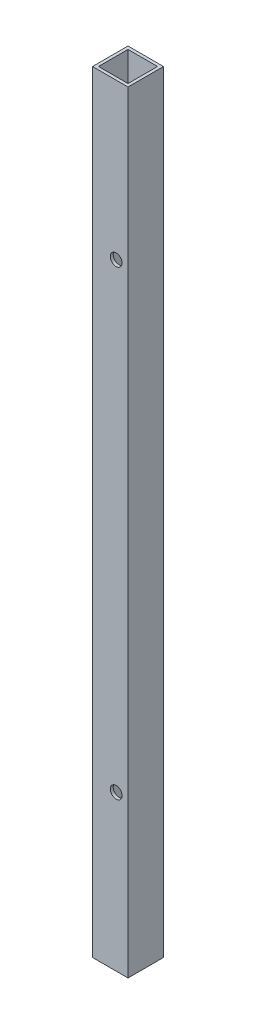
SolidWorks part; units mm, degrees
ref_plane "Front" through (0, 0, 0) normal (0, 0, 1) x (1, 0, 0)
ref_plane "Top" through (0, 0, 0) normal (0, 1, 0) x (1, 0, 0)
ref_plane "Right" through (0, 0, 0) normal (1, 0, 0) x (0, 0, -1)
sketch "Sketch2" plane through (0, 0, 0) normal (0, 1, 0) x (1, 0, 0)
  line L0 (1.5875, 1.5875) -> (17.4625, 1.5875)
  line L1 (0, 0) -> (19.05, 0)
  line L2 (0, 0) -> (0, 19.05)
  line L3 (0, 19.05) -> (19.05, 19.05)
  line L4 (19.05, 0) -> (19.05, 19.05)
  line L5 (17.4625, 1.5875) -> (17.4625, 17.4625)
  line L6 (1.5875, 17.4625) -> (17.4625, 17.4625)
  line L7 (1.5875, 1.5875) -> (1.5875, 17.4625)
extrude "Boss-Extrude1" add sketch "Sketch2" along normal blind 414.3375
sketch "Sketch3" plane through (0, 0, 0) normal (0, 0, 1) x (1, 0, 0)
  circle A0 centre (12.7, 83.1799) radius 3.175 construction
  circle A1 centre (12.7, 330.8299) radius 3.175 construction
  circle A2 centre (12.7, 83.1799) radius 3.175
  circle A3 centre (12.7, 330.8299) radius 3.175
extrude "Cut-Extrude1" cut sketch "Sketch3" against normal through all
